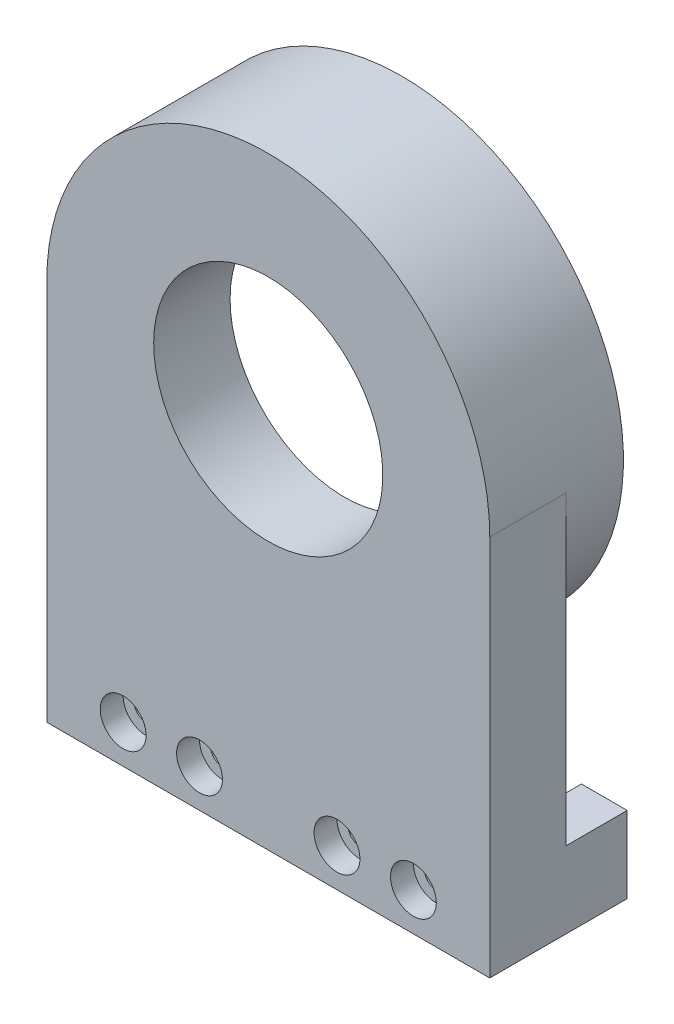
SolidWorks part; units mm, degrees
ref_plane "前视基准面" through (0, 0, 0) normal (0, 0, 1) x (1, 0, 0)
ref_plane "上视基准面" through (0, 0, 0) normal (0, 1, 0) x (1, 0, 0)
ref_plane "右视基准面" through (0, 0, 0) normal (1, 0, 0) x (0, 0, -1)
sketch "草图1" plane through (0, 0, 0) normal (0, 0, 1) x (1, 0, 0)
  line L1 (-29, 25) -> (29, 25)
  line L2 (-29, 25) -> (-29, -25)
  line L3 (-29, -25) -> (29, -25)
  line L4 (29, 25) -> (29, -25)
  line L5 (0, -25) -> (0, 25) construction
  line L6 (-29, 0) -> (29, 0) construction
  arc A0 (-29, 25) -> (29, 25) centre (0, 25) cw
  point P0 (0, 0)
  dimension "D1" = 58
  dimension "D2" = 50
extrude "凸台-拉伸1" add sketch "草图1" along normal blind 10 contours A0 L1 | L4 L1 L2 L3
sketch "草图2" plane through (0, 0, 0) normal (0, 0, -1) x (-1, 0, 0)
  circle A0 centre (0, 25) radius 29
  circle A1 centre (0, 25) radius 26.1
  dimension "D1" = 58
  dimension "D2" = 52.2
extrude "凸台-拉伸2" add sketch "草图2" along normal blind 7.5
sketch "草图3" plane through (0, 0, 0) normal (0, 0, -1) x (-1, 0, 0)
  circle A0 centre (0, 25) radius 24
  circle A2 centre (0, 25) radius 26.1 construction
  circle A3 centre (0, 25) radius 26.1
  dimension "D1" = 48
extrude "凸台-拉伸3" add sketch "草图3" along normal blind 0.5
sketch "草图4" plane through (0, 0, 0) normal (0, 0, -1) x (-1, 0, 0)
  line L0 (0, -1.1) -> (0, -28.635) construction
  line L1 (-35.748, -20) -> (39.5283, -20) construction
  line L2 (29, -25) -> (-29, -25) construction
  line L3 (-29, 25) -> (-29, -25) construction
  line L4 (29, 25) -> (29, -25) construction
  line L5 (-29, -15) -> (-23, -15)
  line L6 (-29, -20) -> (-23, -20)
  line L7 (-29, -20) -> (-29, -25)
  line L8 (-29, -25) -> (-23, -25)
  line L9 (-23, -20) -> (-23, -25)
  line L10 (-23, -20) -> (-23, -15)
  line L11 (-29, -20) -> (-23, -20)
  line L12 (-29, -20) -> (-29, -15)
  line L13 (29, -25) -> (23, -25)
  line L14 (23, -20) -> (23, -25)
  line L15 (29, -20) -> (23, -20)
  line L16 (29, -20) -> (29, -25)
  line L17 (29, -20) -> (29, -15)
  line L18 (29, -20) -> (23, -20)
  line L19 (23, -20) -> (23, -15)
  line L20 (29, -15) -> (23, -15)
  circle A0 centre (0, 25) radius 26.1 construction
  circle A1 centre (0, 25) radius 26.1 construction
  line M2 (-29, 25) -> (-29, -25)
  line M3 (-29, -25) -> (29, -25)
  line M4 (29, -25) -> (29, 25)
  dimension "D1" = 5
  dimension "D2" = 5
  dimension "D3" = 6
extrude "凸台-拉伸4" add sketch "草图4" along normal blind 8 contours L6 L10 L5 M2 | L9 L6 M2 M3 | L20 L19 L15 M4 | L15 L14 M4 M3
sketch "草图5" plane through (0, 0, 0) normal (0, 0, -1) x (-1, 0, 0)
  line L0 (-35.748, -20) -> (39.5283, -20) construction
  line L1 (0, -1.1) -> (0, -28.635) construction
  line L2 (0, -1.1) -> (0, -28.635) construction
  circle A0 centre (-19, -20) radius 1.55
  circle A1 centre (-9, -20) radius 1.55
  circle A2 centre (9, -20) radius 1.55
  circle A3 centre (19, -20) radius 1.55
  dimension "D1" = 3.1
  dimension "D2" = 3.1
  dimension "D3" = 10
  dimension "D4" = 10
extrude "切除-拉伸1" cut sketch "草图5" against normal up to next
sketch "草图6" plane through (0, 0, 10) normal (0, 0, 1) x (1, 0, 0)
  circle A0 centre (19, -20) radius 3
  circle A1 centre (9, -20) radius 3
  circle A2 centre (-9, -20) radius 3
  circle A3 centre (-19, -20) radius 3
  dimension "D1" = 6
extrude "切除-拉伸2" cut sketch "草图6" against normal blind 3
sketch "草图7" plane through (0, 0, 0) normal (0, 0, -1) x (-1, 0, 0)
  circle A0 centre (0, 25) radius 15
  dimension "D1" = 30
extrude "切除-拉伸3" cut sketch "草图7" against normal through all
